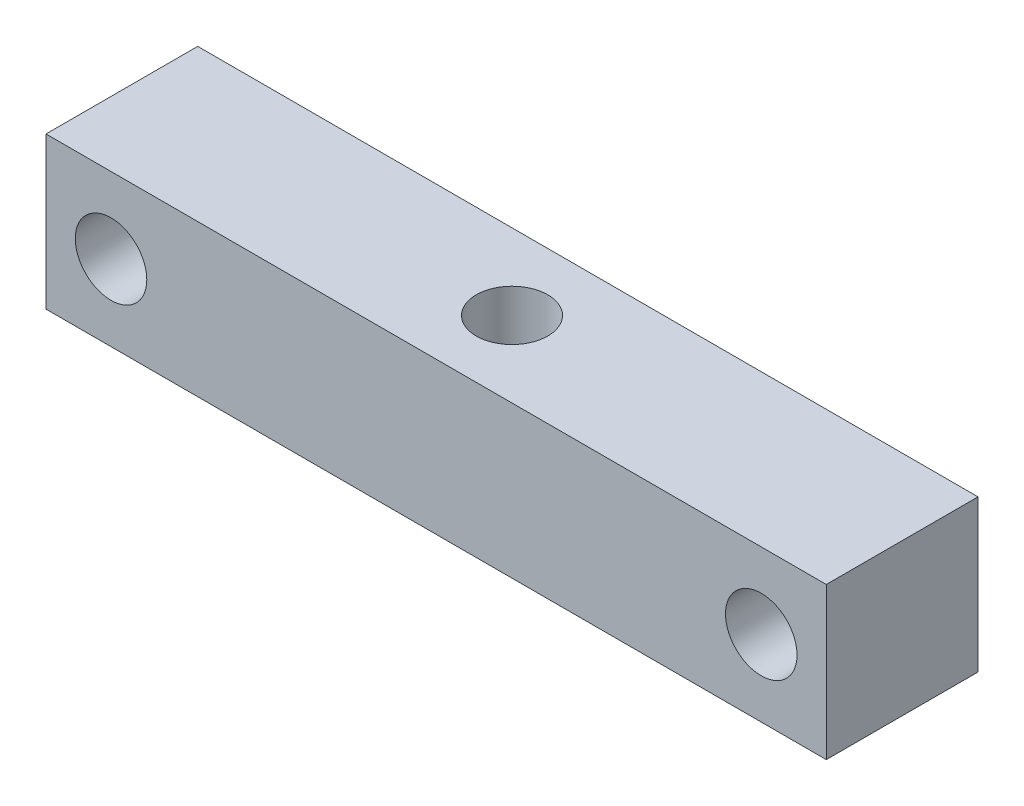
SolidWorks part; units mm, degrees
material "1060 合金"
ref_plane "前视基准面" through (0, 0, 0) normal (0, 0, 1) x (1, 0, 0)
ref_plane "上视基准面" through (0, 0, 0) normal (0, 1, 0) x (1, 0, 0)
ref_plane "右视基准面" through (0, 0, 0) normal (1, 0, 0) x (0, 0, -1)
other "Configuration Table"
sketch "草图1" plane through (0, 0, 0) normal (0, 0, 1) x (1, 0, 0)
  line L0 (-15, 0) -> (15, 0) construction
  line L2 (18, -3.5) -> (-18, -3.5)
  line L3 (18, -3.5) -> (18, 3.5)
  line L4 (18, 3.5) -> (-18, 3.5)
  line L5 (-18, -3.5) -> (-18, 3.5)
  line L6 (18, -3.5) -> (-18, 3.5) construction
  line L7 (18, 3.5) -> (-18, -3.5) construction
  circle A1 centre (-15, 0) radius 0.5
  circle A2 centre (-15, 0) radius 2 construction
  circle A3 centre (15, 0) radius 0.5
  point P5 (0, 0)
  point P8 (0, 0)
  dimension "D1" = 4
  dimension "D2" = 1
  dimension "D4" = 3
  dimension "D5" = 3.5
  dimension "D3" = 30
extrude "凸台-拉伸1" add sketch "草图1" along normal mid plane 7
hole_wizard "M4 螺纹孔1" positions "草图2" profile "草图3" tap size "M4" standard "GB"
sketch "草图2" plane through (0, 0, 3.5) normal (0, 0, 1) x (1, 0, 0)
  point P0 (-15, 0)
  point P3 (15, 0)
sketch "草图3" plane through (-15, 0, 3.5) normal (1, 0, 0) x (0, -1, 0)
  line L0 (0, 0) -> (0, 23.0914)
  line L1 (0, 23.0914) -> (1.65, 22.1)
  line L2 (1.65, 22.1) -> (1.65, 0)
  line L5 (1.65, 0) -> (0, 0)
  line L10 (0, 23.0914) -> (-1.65, 22.1) construction
  line L11 (0, -6.35) -> (0, 107.95) construction
  dimension "螺纹孔钻头直径" = 3.3
  dimension "螺纹孔钻头深度" = 22.1
  dimension "导头角度" = 118
cosmetic thread "孔螺蚊线1" parameters "D1"=20, "D2"=4
cosmetic thread "孔螺蚊线2" parameters "D1"=20, "D2"=4
hole_wizard "M4 螺纹孔2" positions "草图5" profile "草图6" tap size "M4" standard "GB"
sketch "草图5" plane through (0, 3.5, 0) normal (0, 1, 0) x (1, 0, 0)
  point P0 (0, 0)
sketch "草图6" plane through (0, 3.5, 0) normal (1, 0, 0) x (0, 0, 1)
  line L0 (0, 0) -> (0, 23.0914)
  line L1 (0, 23.0914) -> (1.65, 22.1)
  line L2 (1.65, 22.1) -> (1.65, 0)
  line L5 (1.65, 0) -> (0, 0)
  line L10 (0, 23.0914) -> (-1.65, 22.1) construction
  line L11 (0, -6.35) -> (0, 107.95) construction
  dimension "螺纹孔钻头直径" = 3.3
  dimension "螺纹孔钻头深度" = 22.1
  dimension "导头角度" = 118
cosmetic thread "孔螺蚊线3" parameters "D1"=20, "D2"=4
